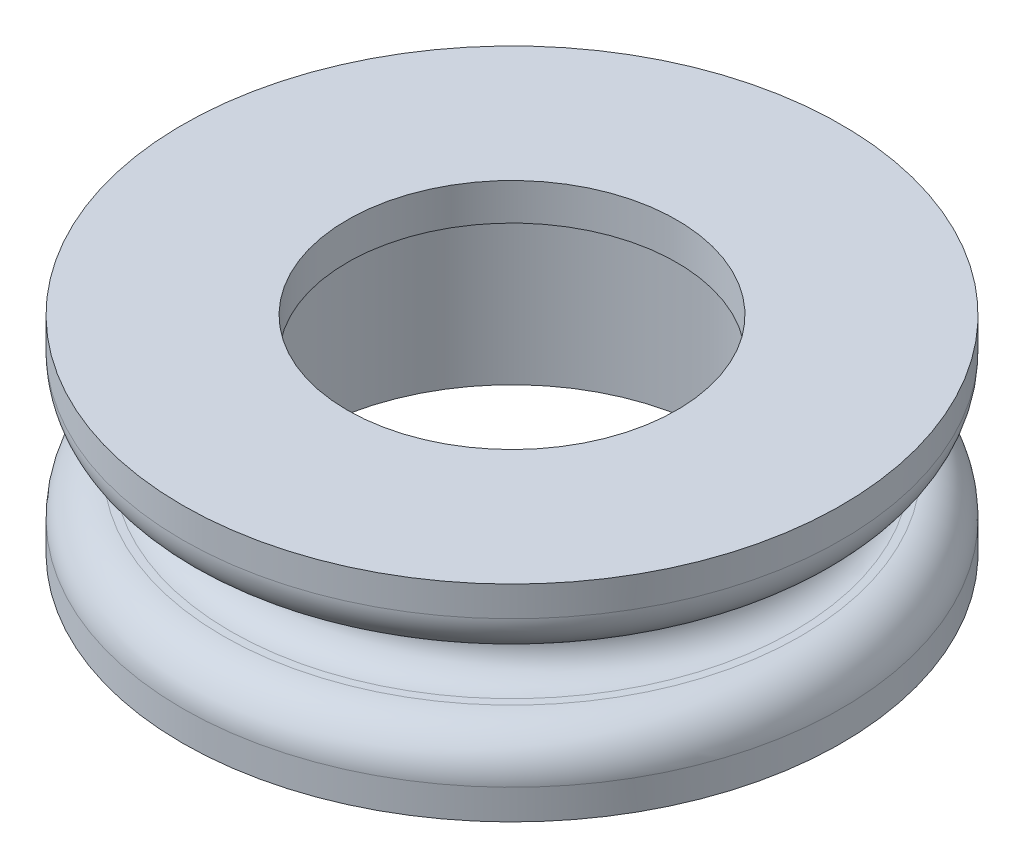
SolidWorks part; units mm, degrees
ref_plane "Front Plane" through (0, 0, 0) normal (0, 0, 1) x (1, 0, 0)
ref_plane "Top Plane" through (0, 0, 0) normal (0, 1, 0) x (1, 0, 0)
ref_plane "Right Plane" through (0, 0, 0) normal (1, 0, 0) x (0, 0, -1)
sketch "Sketch2" plane through (0, 0, 0) normal (1, 0, 0) x (0, 0, -1)
  line L0 (0, 16.0431) -> (0, -18.032) construction
  line L1 (8.89, 5.5575) -> (8.89, 3.5687)
  line L2 (8.89, 3.5687) -> (11.1125, 3.5687)
  line L3 (11.1125, 3.5687) -> (11.1125, -5.5575)
  line L4 (11.1125, -5.5575) -> (17.78, -5.5575)
  line L5 (17.78, -5.5575) -> (17.78, -1.7399)
  line L6 (17.78, -1.7399) -> (13.6397, -1.5773)
  line L7 (13.6397, -1.5773) -> (13.6397, 1.5773)
  line L8 (13.6397, 1.5773) -> (17.78, 1.7399)
  line L9 (17.78, 1.7399) -> (17.78, 5.5575)
  line L10 (17.78, 5.5575) -> (8.89, 5.5575)
  line L11 (13.6397, 1.5773) -> (13.6397, 5.5575) construction
  line L12 (13.6397, -1.5773) -> (13.6397, -5.5575) construction
  point P5 (13.6397, 0)
  point P14 (17.78, 3.6487)
  dimension "D1" = 1.9888
  dimension "D2" = 3.4798
  dimension "D3" = 3.8176
  dimension "D4" = 17.78
  dimension "D5" = 2.2225
  dimension "D6" = 6.6675
  dimension "D7" = 8.89
  dimension "D8" = 3.9802
  dimension "D9" = 4.1435
revolve "Revolve1" add sketch "Sketch2" angle 360 about L0
fillet "Fillet5" radius 2.286 2 edges at (0, -1.7399, 17.78) (0, 1.7399, 17.78)
fillet "Fillet6" radius 1.6002 2 edges at (0, -1.5773, 13.6397) (0, 1.5773, 13.6397)
